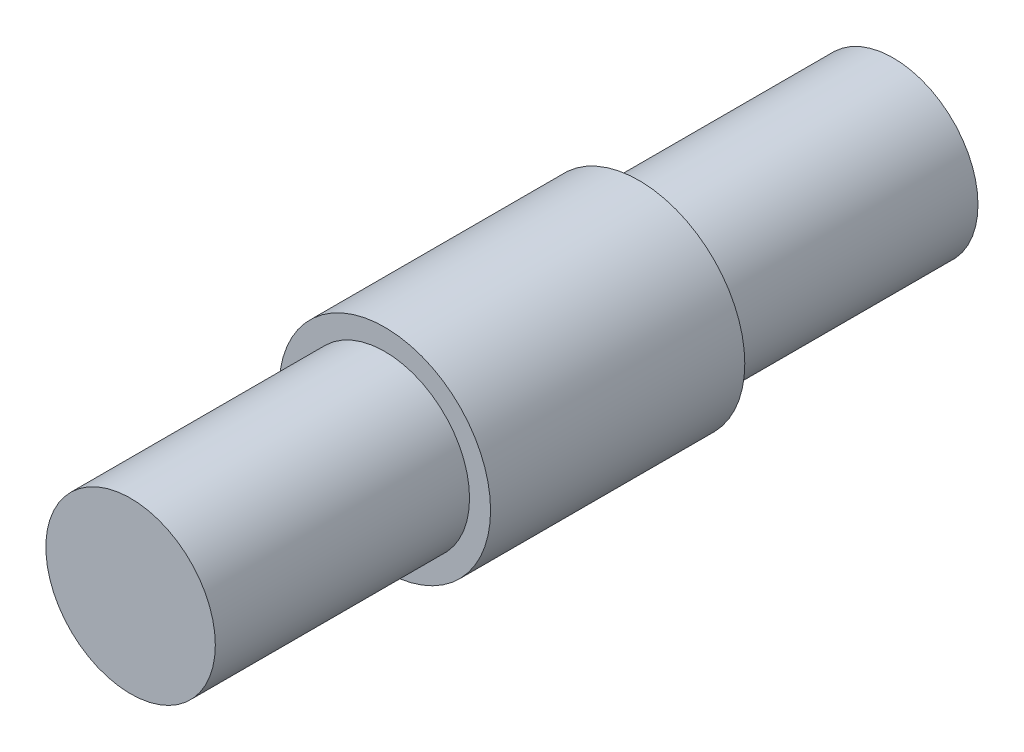
SolidWorks part; units mm, degrees
ref_plane "Front Plane" through (0, 0, 0) normal (0, 0, 1) x (1, 0, 0)
ref_plane "Top Plane" through (0, 0, 0) normal (0, 1, 0) x (1, 0, 0)
ref_plane "Right Plane" through (0, 0, 0) normal (1, 0, 0) x (0, 0, -1)
sketch "Sketch1" plane through (0, 0, 0) normal (0, 0, 1) x (1, 0, 0)
  circle A0 centre (0, 0) radius 3.9624
  dimension "D1" = 7.9248
extrude "Boss-Extrude1" add sketch "Sketch1" along normal mid plane 9.525
sketch "Sketch2" plane through (0, 0, 0) normal (0, 0, 1) x (1, 0, 0)
  circle A0 centre (0, 0) radius 3.175
  dimension "D1" = 6.35
extrude "Boss-Extrude2" add sketch "Sketch2" along normal mid plane 28.575
